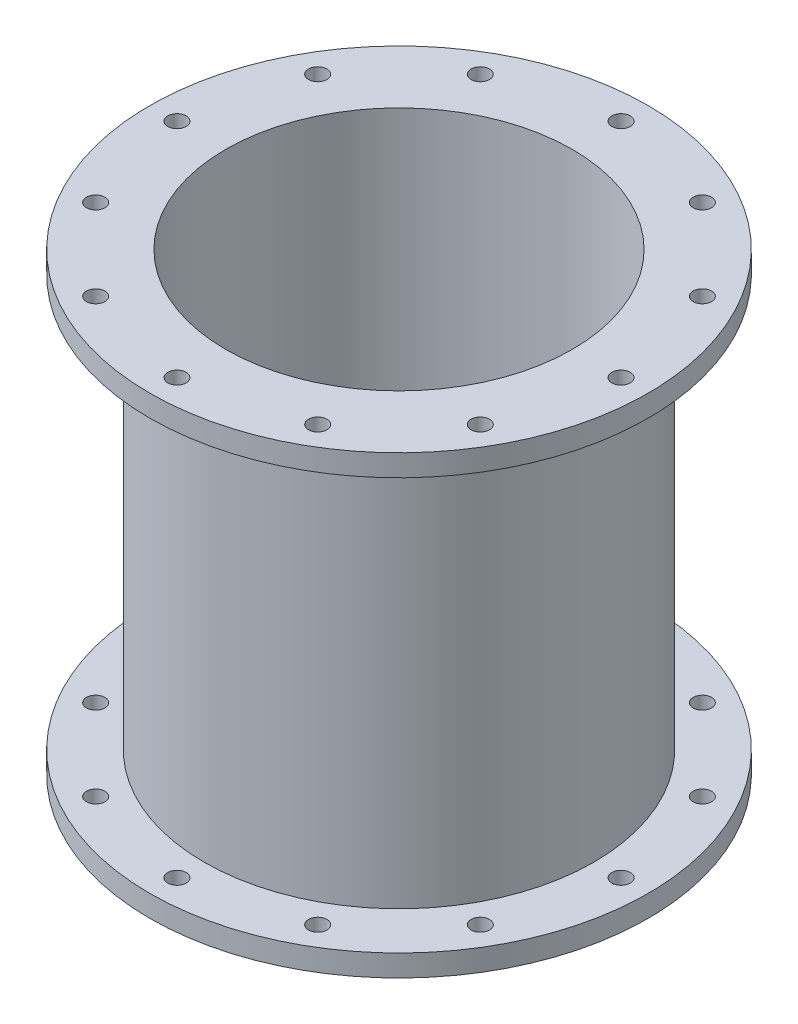
SolidWorks part; units mm, degrees
material "AISI 316 Annealed Stainless Steel Bar (SS)"
ref_plane "Front Plane" through (0, 0, 0) normal (0, 0, 1) x (1, 0, 0)
ref_plane "Top Plane" through (0, 0, 0) normal (0, 1, 0) x (1, 0, 0)
ref_plane "Right Plane" through (0, 0, 0) normal (1, 0, 0) x (0, 0, -1)
sketch "Sketch1" plane through (0, 0, 0) normal (0, 0, 1) x (1, 0, 0)
  line L0 (-32, 0) -> (-46, 0)
  line L1 (-46, 0) -> (-46, 4)
  line L2 (-46, 4) -> (-36, 4)
  line L3 (-36, 4) -> (-36, 79.984)
  line L4 (-36, 79.984) -> (-46, 79.984)
  line L5 (-46, 79.984) -> (-46, 83.984)
  line L6 (-46, 83.984) -> (-32, 83.984)
  line L7 (-32, 83.984) -> (-32, 0)
  line L8 (0, 0) -> (0, 16.0379)
  dimension "D1" = 32
  dimension "D2" = 46
  dimension "D3" = 4
  dimension "D4" = 4
  dimension "D5" = 83.984
  dimension "D6" = 4
  dimension "D7" = 46
revolve "Revolve1" add sketch "Sketch1" angle 360 about L8
sketch "Sketch2" plane through (0, 83.984, 0) normal (0, 1, 0) x (1, 0, 0)
  line L0 (0, 0) -> (0, 46)
  circle A0 centre (0, 0) radius 46 construction
  circle A1 centre (0, 41) radius 1.975
  dimension "D1" = 5
hole_wizard "M3 Clearance Hole1" positions "Sketch4" profile "Sketch3" hole size "M3" standard "ANSI Metric" end condition up to next
sketch "Sketch4" plane through (0, 83.984, 0) normal (0, 1, 0) x (1, 0, 0)
  point P0 (0, 41)
sketch "Sketch3" plane through (0, 83.984, -41) normal (1, 0, 0) x (0, 0, 1)
  line L0 (0, 0) -> (0, 4.001)
  line L1 (0, 4.001) -> (1.7, 4.001)
  line L2 (1.7, 4.001) -> (1.7, 0)
  line L5 (1.7, 0) -> (0, 0)
  line L11 (0, -6.35) -> (0, 107.95) construction
  dimension "Thru Hole Dia." = 3.4
  dimension "Thru Hole Depth" = 4.001
sketch "Sketch5" plane through (0, 0, 0) normal (0, -1, 0) x (1, 0, 0)
  line L0 (0, 0) -> (0, -46) construction
  line L1 (0, 0) -> (0, -46)
  circle A0 centre (0, -41) radius 1.975 construction
  circle A1 centre (0, -41) radius 1.975
hole_wizard "M3 Clearance Hole2" positions "Sketch7" profile "Sketch6" hole size "M3" standard "ANSI Metric" end condition up to next
sketch "Sketch7" plane through (0, 0, 0) normal (0, -1, 0) x (-1, 0, 0)
  point P0 (0, 41)
sketch "Sketch6" plane through (0, 0, -41) normal (1, 0, 0) x (0, 0, -1)
  line L0 (0, 0) -> (0, 4.001)
  line L1 (0, 4.001) -> (1.7, 4.001)
  line L2 (1.7, 4.001) -> (1.7, 0)
  line L5 (1.7, 0) -> (0, 0)
  line L11 (0, -6.35) -> (0, 107.95) construction
  dimension "Thru Hole Dia." = 3.4
  dimension "Thru Hole Depth" = 4.001
pattern_circular "CirPattern1" count 12 over 360 about axis through (0, 0, 0) along (0, 1, 0) of "M3 Clearance Hole1", "M3 Clearance Hole2"
equation "\"r_cc_inner\"= 10'combustion chamber inner radius [mm]"
equation "\"r_cc_outer\"= 24'combustion chamber outer radius [mm]"
equation "\"L_star\"= 1500'combustion process characteristic length [mm]"
equation "\"At\"= 0.0000598 * ( 1000 ) ^ 2'Throat Area [mm^2]"
equation "\"x_cc\"= \"L_star\" * \"At\" / ( pi * ( \"r_cc_outer\" ^ 2 - \"r_cc_inner\" ^ 2 ) )'combustion chamber physical length [mm]"
equation "\"x_convergent\"= 20'length of the convergent section of the nozzle [mm]"
equation "\"r_throat\"= 15'outer radius of throat gap [mm]"
equation "\"x_material_change\"= 1.5 * \"r_throat\"'distance below throat at which nozzle material changes to a low-temp material [mm]"
equation "\"t_i\"= 8'insulation thickness required by thermal considerations [mm]"
equation "\"t_cw\"= 4'pressure vessle cylinder wall thickness required by structural considerations [mm]"
equation "\"t_p\" = 1 / 4 * 25.4'pressure vessle plate thickness required by structural considerations [mm]"
equation "\"r_outer\"= \"r_cc_outer\" + \"t_i\" + \"t_cw\" + 10'overall outermost radius of engine [mm]"
equation "\"r_rod\"= 1 / 8 * 25.4 / 2'radius of the threaded rod in the center fo the spike [mm]"
equation "\"D1@Sketch1\"=\"r_cc_outer\" + \"t_i\""
equation "\"D2@Sketch1\"=\"r_outer\""
equation "\"D3@Sketch1\"=\"t_cw\""
equation "\"D4@Sketch1\"=\"t_cw\""
equation "\"D6@Sketch1\"=\"t_cw\""
equation "\"D5@Sketch1\"=\"t_i\"/2 + \"x_convergent\" + \"x_cc\""
equation "\"D7@Sketch1\"=\"r_outer\""
